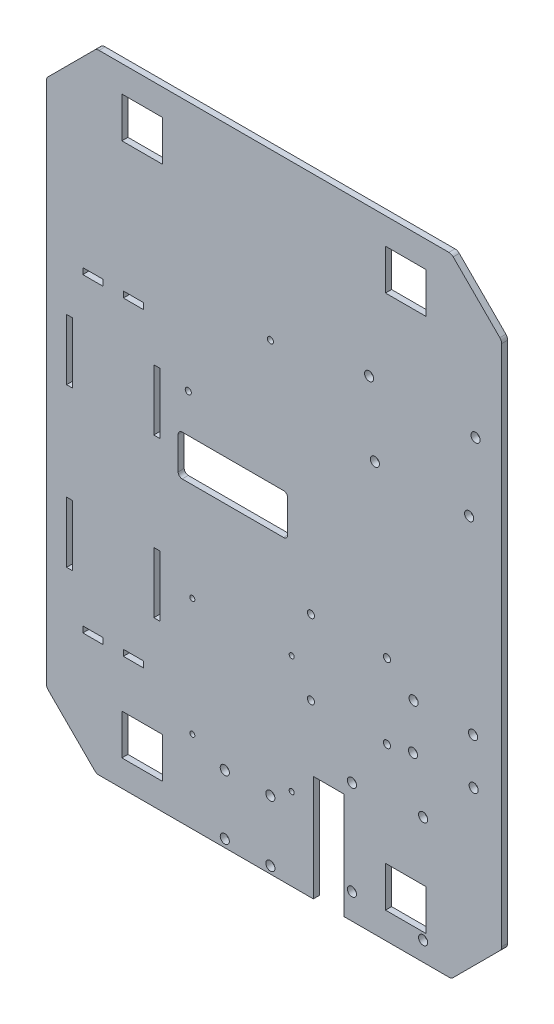
SolidWorks part; units mm, degrees
material "Alliage 1060"
ref_plane "Plan de dessus" through (0, 0, 0) normal (0, 0, 1) x (1, 0, 0)
ref_plane "Plan de droite" through (0, 0, 0) normal (0, 1, 0) x (1, 0, 0)
ref_plane "Plan de face" through (0, 0, 0) normal (1, 0, 0) x (0, 0, -1)
sketch "Esquisse1" plane through (0, 0, 0) normal (0, 0, 1) x (1, 0, 0)
  line L0 (0, 0) -> (-175, 0)
  line L1 (-175, 0) -> (-199.7487, 24.7487)
  line L2 (-199.7487, 24.7487) -> (-199.7487, 284.7487)
  line L3 (-199.7487, 284.7487) -> (-175, 309.4975)
  line L4 (-175, 309.4975) -> (0, 309.4975)
  line L5 (0, 309.4975) -> (24.7487, 284.7487)
  line L6 (24.7487, 284.7487) -> (24.7487, 24.7487)
  line L7 (24.7487, 24.7487) -> (0, 0)
  dimension "D1" = 260
  dimension "D2" = 35
  dimension "D3" = 135
  dimension "D4" = 175
extrude "Base" add sketch "Esquisse1" along normal blind 3
sketch "Esquisse2" plane through (0, 0, 3) normal (0, 0, 1) x (1, 0, 0)
  line L0 (-87.5, 309.4975) -> (-87.5, 0) construction
  line L5 (0, 309.4975) -> (-175, 309.4975) construction
  line L6 (-175, 0) -> (0, 0) construction
  line L7 (-199.7487, 154.7487) -> (24.7487, 154.7487) construction
  line L8 (-199.7487, 284.7487) -> (-199.7487, 24.7487) construction
  line L9 (24.7487, 24.7487) -> (24.7487, 284.7487) construction
  line L10 (-162.5, 13) -> (-142.5, 33) construction
  line L11 (-162.5, 276.4975) -> (-142.5, 276.4975)
  line L12 (-162.5, 276.4975) -> (-162.5, 296.4975)
  line L13 (-162.5, 296.4975) -> (-142.5, 296.4975)
  line L14 (-142.5, 276.4975) -> (-142.5, 296.4975)
  line L15 (-162.5, 276.4975) -> (-142.5, 296.4975) construction
  line L16 (-162.5, 296.4975) -> (-142.5, 276.4975) construction
  line L17 (-162.5, 33) -> (-142.5, 13) construction
  line L18 (-162.5, 13) -> (-142.5, 13)
  line L19 (-162.5, 33) -> (-162.5, 13)
  line L20 (-162.5, 33) -> (-142.5, 33)
  line L21 (-142.5, 33) -> (-142.5, 13)
  line L22 (-12.5, 13) -> (-32.5, 13)
  line L23 (-12.5, 33) -> (-32.5, 33)
  line L24 (-32.5, 33) -> (-32.5, 13)
  line L25 (-12.5, 33) -> (-32.5, 13) construction
  line L26 (-12.5, 13) -> (-32.5, 33) construction
  line L27 (-12.5, 33) -> (-12.5, 13)
  line L28 (-32.5, 276.4975) -> (-32.5, 296.4975)
  line L29 (-12.5, 276.4975) -> (-32.5, 296.4975) construction
  line L30 (-12.5, 296.4975) -> (-32.5, 276.4975) construction
  line L31 (-12.5, 276.4975) -> (-32.5, 276.4975)
  line L32 (-12.5, 276.4975) -> (-12.5, 296.4975)
  line L33 (-12.5, 296.4975) -> (-32.5, 296.4975)
  point P0 (-152.5, 286.4975)
  dimension "D1" = 20
  dimension "D2" = 65
  dimension "D3" = 23
extrude "Enlèv. mat.-Extru.1" cut sketch "Esquisse2" against normal through all
fillet "Congé1" radius 3 8 edges at (-199.7487, 24.7487, 1.5) (-175, 0, 1.5) (0, 0, 1.5) (24.7487, 24.7487, 1.5) (24.7487, 284.7487, 1.5) (0, 309.4975, 1.5) (-175, 309.4975, 1.5) (-199.7487, 284.7487, 1.5)
sketch "Esquisse4" plane through (0, 0, 3) normal (0, 0, 1) x (1, 0, 0)
  line L5 (-82.7487, 166.9975) -> (-132.7487, 166.9975)
  line L8 (-80.7487, 164.9975) -> (-80.7487, 148.9975)
  line L9 (-82.7487, 146.9975) -> (-132.7487, 146.9975)
  line L13 (-134.7487, 164.9975) -> (-134.7487, 148.9975)
  line L14 (-199.7487, 283.5061) -> (-199.7487, 25.9914) construction
  line L15 (-23, 25.5164) -> (-23, 0) construction
  line L16 (-173.7574, 0) -> (-1.2426, 0) construction
  circle A0 centre (-78.7487, 98.4975) radius 1.25
  circle A1 centre (-127.7487, 98.4975) radius 1.25
  circle A2 centre (-78.7487, 40.4975) radius 1.25
  circle A3 centre (-127.7487, 40.4975) radius 1.25
  circle A4 centre (-129.7487, 185.9975) radius 1.5
  circle A5 centre (-89.2487, 227.9975) radius 1.5
  arc A6 (-80.7487, 164.9975) -> (-82.7487, 166.9975) centre (-82.7487, 164.9975) ccw
  arc A7 (-82.7487, 146.9975) -> (-80.7487, 148.9975) centre (-82.7487, 148.9975) ccw
  arc A8 (-134.7487, 148.9975) -> (-132.7487, 146.9975) centre (-132.7487, 148.9975) ccw
  arc A9 (-134.7487, 164.9975) -> (-132.7487, 166.9975) centre (-132.7487, 164.9975) cw
  point P8 (-80.7487, 146.9975)
  dimension "D2" = 65
  dimension "D3" = 55.7487
  dimension "D4" = 3
  dimension "D5" = 50
  dimension "D6" = 104.7487
  dimension "D7" = 40.4975
  dimension "D9" = 2
  dimension "D10" = 2
extrude "Enlèv. mat.-Extru.4" cut sketch "Esquisse4" against normal through all
sketch "Esquisse5" plane through (0, 0, 3) normal (0, 0, 1) x (1, 0, 0)
  line L0 (-68.0934, 52.3226) -> (-53.0623, 52.3226)
  line L1 (-53.0623, 52.3226) -> (-53.0623, 0)
  line L2 (-173.7574, 0) -> (-1.2426, 0) construction
  line L3 (-53.0623, 0) -> (-68.0934, 0)
  line L4 (-68.0934, 0) -> (-68.0934, 52.3226)
  line L5 (24.7487, 25.9914) -> (24.7487, 283.5061) construction
  line L6 (-12.5, 13) -> (-12.5, 33) construction
  line L7 (-32.5, 13) -> (-12.5, 13) construction
  line L9 (-79.2513, 181.3816) -> (-79.2513, 125.3816) construction
  line L22 (-79.2513, 153.3816) -> (-38.4877, 153.3816) construction
  line L40 (-25, 246.9975) -> (-25, 215.8484) construction
  line L41 (-44.2513, 227.8816) -> (-41, 227.8816) construction
  line L50 (4.7487, 72.3816) -> (24.7487, 72.3816) construction
  line L51 (4.7487, 72.3816) -> (4.7487, -6.8318) construction
  line L52 (-111.7384, 3.8325) -> (-121.6077, 3.8325) construction
  line L53 (-121.6077, 3.8325) -> (-121.6077, 6.4524) construction
  line L54 (-18.656, 109.4514) -> (-18.656, 119.3207) construction
  line L55 (-18.656, 119.3207) -> (-16.0361, 119.3207) construction
  line L56 (-13.95, 61.9819) -> (-13.95, 86.9819) construction
  line L57 (-1.2426, 309.4975) -> (-173.7574, 309.4975) construction
  circle A0 centre (-111.7384, 3.8325) radius 2.25
  circle A1 centre (-89.2689, 3.5385) radius 2.25
  circle A2 centre (-89.2689, 33.4615) radius 2.25
  circle A3 centre (-111.7384, 33.1675) radius 2.25
  circle A4 centre (-49.05, 12.6409) radius 2.25
  circle A5 centre (-13.95, 9.5) radius 2.25
  circle A6 centre (-49.05, 59.1409) radius 2.25
  circle A7 centre (-13.95, 61.9819) radius 2.25
  circle A8 centre (8.7487, 201.8975) radius 2.25
  circle A9 centre (11.8897, 236.9975) radius 2.25
  circle A10 centre (-37.7513, 201.8975) radius 2.25
  circle A11 centre (-40.5922, 236.9975) radius 2.25
  circle A12 centre (-18.656, 109.4514) radius 2.25
  circle A13 centre (-18.95, 86.9819) radius 2.25
  circle A14 centre (10.9731, 86.9819) radius 2.25
  circle A15 centre (10.6791, 109.4514) radius 2.25
  dimension "D1" = 4.5
  dimension "D2" = 4.5
  dimension "D3" = 46.5
  dimension "D4" = 52.4819
  dimension "D5" = 3.1409
  dimension "D6" = 16
  dimension "D7" = 72.5
  dimension "D8" = 35.1
extrude "Enlèv. mat.-Extru.5" cut sketch "Esquisse5" against normal up to next
sketch "Esquisse7" plane through (0, 0, 3) normal (0, 0, 1) x (1, 0, 0)
  circle A0 centre (6.4987, 233.5269) radius 2
  circle A1 centre (6.4987, 218.3975) radius 2
  dimension "D1" = 4
sketch "cagetteù" plane through (0, 0, 3) normal (0, 0, 1) x (1, 0, 0)
  line L0 (-199.7487, 154.7487) -> (-189.7487, 154.7487) construction
  line L1 (-199.7487, 283.5061) -> (-199.7487, 25.9914) construction
  line L2 (-189.7487, 294.7487) -> (-189.7487, 14.7487) construction
  line L3 (-198.8701, 23.8701) -> (-175.8787, 0.8787) construction
sketch "PONT H mal place" plane through (0, 0, 3) normal (0, 0, 1) x (1, 0, 0)
  circle A0 centre (-69.2625, 120.9474) radius 1.75
  circle A1 centre (-69.2625, 84.2056) radius 1.75
  circle A2 centre (-31.7762, 84.2056) radius 1.75
  circle A3 centre (-31.7762, 120.9474) radius 1.75
  dimension "D1" = 3.5
extrude "pont_H_mal_place" cut sketch "PONT H mal place" against normal blind 3
sketch "Esquisse10" plane through (0, 0, 3) normal (0, 0, 1) x (1, 0, 0)
  line L0 (-181.7487, 56.7487) -> (-171.7487, 56.7487)
  line L1 (-171.7487, 56.7487) -> (-171.7487, 59.7487)
  line L2 (-171.7487, 59.7487) -> (-181.7487, 59.7487)
  line L3 (-181.7487, 59.7487) -> (-181.7487, 56.7487)
  line L4 (-186.7487, 80.7487) -> (-189.7487, 80.7487)
  line L5 (-189.7487, 80.7487) -> (-189.7487, 110.7487)
  line L6 (-189.7487, 110.7487) -> (-186.7487, 110.7487)
  line L7 (-186.7487, 110.7487) -> (-186.7487, 80.7487)
  line L8 (-151.7487, 56.7487) -> (-151.7487, 59.7487)
  line L9 (-151.7487, 59.7487) -> (-161.7487, 59.7487)
  line L10 (-161.7487, 59.7487) -> (-161.7487, 56.7487)
  line L11 (-161.7487, 56.7487) -> (-151.7487, 56.7487)
  line L12 (-143.7487, 80.7487) -> (-146.7487, 80.7487)
  line L13 (-146.7487, 80.7487) -> (-146.7487, 110.7487)
  line L14 (-146.7487, 110.7487) -> (-143.7487, 110.7487)
  line L15 (-143.7487, 110.7487) -> (-143.7487, 80.7487)
  line L16 (-186.7487, 158.7487) -> (-189.7487, 158.7487)
  line L17 (-189.7487, 158.7487) -> (-189.7487, 188.7487)
  line L18 (-186.7487, 158.7487) -> (-186.7487, 188.7487)
  line L19 (-186.7487, 188.7487) -> (-189.7487, 188.7487)
  line L20 (-161.7487, 209.7487) -> (-151.7487, 209.7487)
  line L21 (-151.7487, 209.7487) -> (-151.7487, 212.7487)
  line L22 (-151.7487, 212.7487) -> (-161.7487, 212.7487)
  line L23 (-161.7487, 212.7487) -> (-161.7487, 209.7487)
  line L24 (-171.7487, 209.7487) -> (-181.7487, 209.7487)
  line L25 (-181.7487, 209.7487) -> (-181.7487, 212.7487)
  line L26 (-181.7487, 212.7487) -> (-171.7487, 212.7487)
  line L27 (-171.7487, 212.7487) -> (-171.7487, 209.7487)
  line L28 (-143.7487, 158.7487) -> (-146.7487, 158.7487)
  line L29 (-146.7487, 158.7487) -> (-146.7487, 188.7487)
  line L30 (-146.7487, 188.7487) -> (-143.7487, 188.7487)
  line L31 (-143.7487, 188.7487) -> (-143.7487, 158.7487)
  line L32 (-189.7487, 158.7487) -> (-189.7487, 110.7487) construction
extrude "Enlèv. mat.-Extru.7" cut sketch "Esquisse10" against normal blind 3
